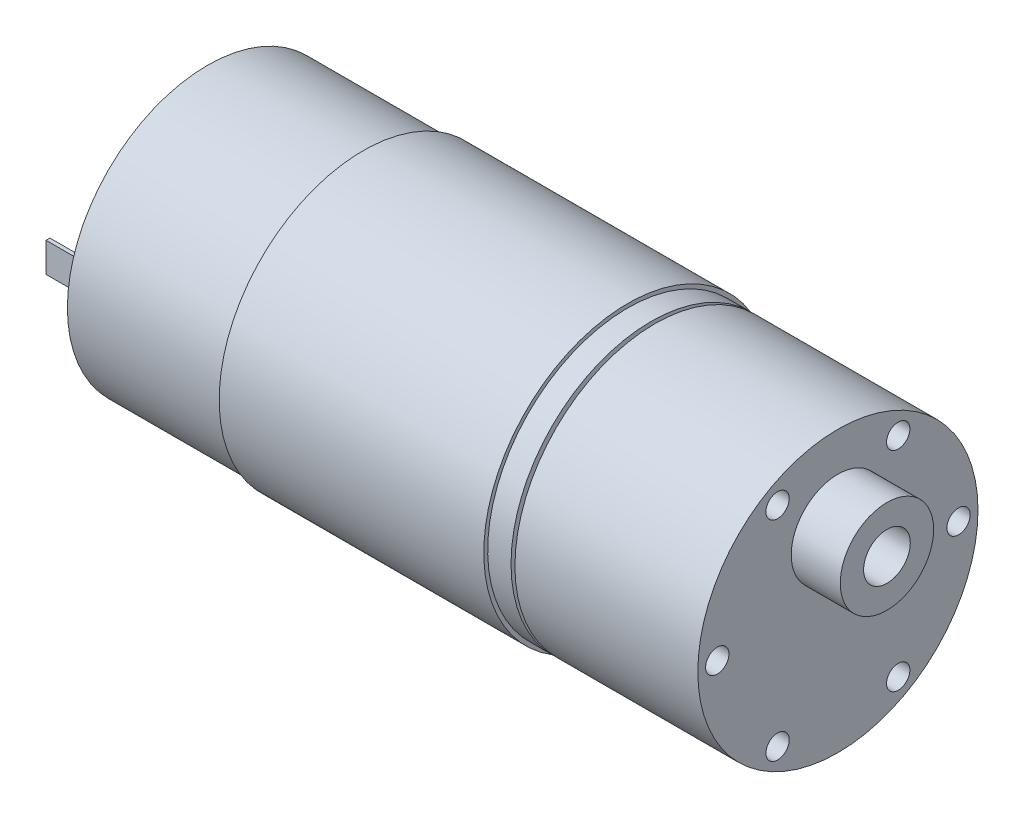
SolidWorks part; units mm, degrees
ref_plane "Front Plane" through (0, 0, 0) normal (0, 0, 1) x (1, 0, 0)
ref_plane "Top Plane" through (0, 0, 0) normal (0, 1, 0) x (1, 0, 0)
ref_plane "Right Plane" through (0, 0, 0) normal (1, 0, 0) x (0, 0, -1)
sketch "Sketch1" plane through (0, 0, 0) normal (1, 0, 0) x (0, 0, -1)
  circle A0 centre (0, 0) radius 18
extrude "Boss-Extrude1" add sketch "Sketch1" along normal blind 57
sketch "Sketch2" plane through (57, 0, 0) normal (1, 0, 0) x (0, 0, -1)
  circle A0 centre (0, 0) radius 17
extrude "Boss-Extrude2" add sketch "Sketch2" along normal blind 0.5
sketch "Sketch3" plane through (57.5, 0, 0) normal (1, 0, 0) x (0, 0, -1)
  circle A0 centre (0, 0) radius 18
extrude "Boss-Extrude3" add sketch "Sketch3" along normal blind 23.5
sketch "Sketch4" plane through (81, 0, 0) normal (1, 0, 0) x (0, 0, -1)
  line L0 (0, 0) -> (0, 7) construction
  circle A0 centre (0, 7) radius 6
  circle A1 centre (0, 7) radius 3
extrude "Boss-Extrude4" add sketch "Sketch4" along normal blind 6.3
sketch "Sketch6" plane through (81, 0, 0) normal (1, 0, 0) x (0, 0, -1)
  line L0 (0, 0) -> (-15.5, 0) construction
  circle A0 centre (-15.5, 0) radius 1.5
  circle A1 centre (-7.75, 13.4234) radius 1.5
  circle A2 centre (7.75, 13.4234) radius 1.5
  circle A3 centre (15.5, 0) radius 1.5
  circle A4 centre (7.75, -13.4234) radius 1.5
  circle A5 centre (-7.75, -13.4234) radius 1.5
  point P17 (0, 0)
  dimension "D1" = 6
extrude "Cut-Extrude1" cut sketch "Sketch6" against normal blind 3.5
sketch "Sketch7" plane through (0, 0, 0) normal (-1, 0, 0) x (0, 0, 1)
  circle A0 centre (0, 0) radius 5.5
extrude "Boss-Extrude6" add sketch "Sketch7" along normal blind 2
sketch "Sketch8" plane through (-2, 0, 0) normal (-1, 0, 0) x (0, 0, 1)
  circle A0 centre (0, 0) radius 1.5
extrude "Boss-Extrude7" add sketch "Sketch8" along normal blind 9
sketch "Sketch9" plane through (0, 0, 0) normal (-1, 0, 0) x (0, 0, 1)
  line L0 (0, 0) -> (13.25, 0) construction
  line L1 (13.25, 1.9) -> (13.25, -1.9)
  line L2 (13.25, 1.9) -> (13.75, 1.9)
  line L3 (13.75, 1.9) -> (13.75, -1.9)
  line L4 (13.75, -1.9) -> (13.25, -1.9)
  line L5 (0, 0) -> (-13.1845, 0) construction
  line L6 (-13.1845, 1.9) -> (-13.1845, -1.9)
  line L7 (-13.1845, -1.9) -> (-13.6845, -1.9)
  line L8 (-13.6845, -1.9) -> (-13.6845, 1.9)
  line L9 (-13.6845, 1.9) -> (-13.1845, 1.9)
extrude "Boss-Extrude8" add sketch "Sketch9" along normal blind 7
ref_plane "Plane1" through (54, 0, 0) normal (1, 0, 0) x (0, 0, -1)
sketch "Sketch10" plane through (54, 0, 0) normal (1, 0, 0) x (0, 0, -1)
  line L2 (2.8813, -17.7679) -> (2.9613, -18.2615)
  line L4 (-2.9613, -18.2615) -> (-2.8813, -17.7679)
  arc A1 (2.8813, -17.7679) -> (-2.8813, -17.7679) centre (0, 0) ccw
  arc A2 (2.9613, -18.2615) -> (-2.9613, -18.2615) centre (0, 0) ccw
extrude "Boss-Extrude9" add sketch "Sketch10" against normal blind 34
